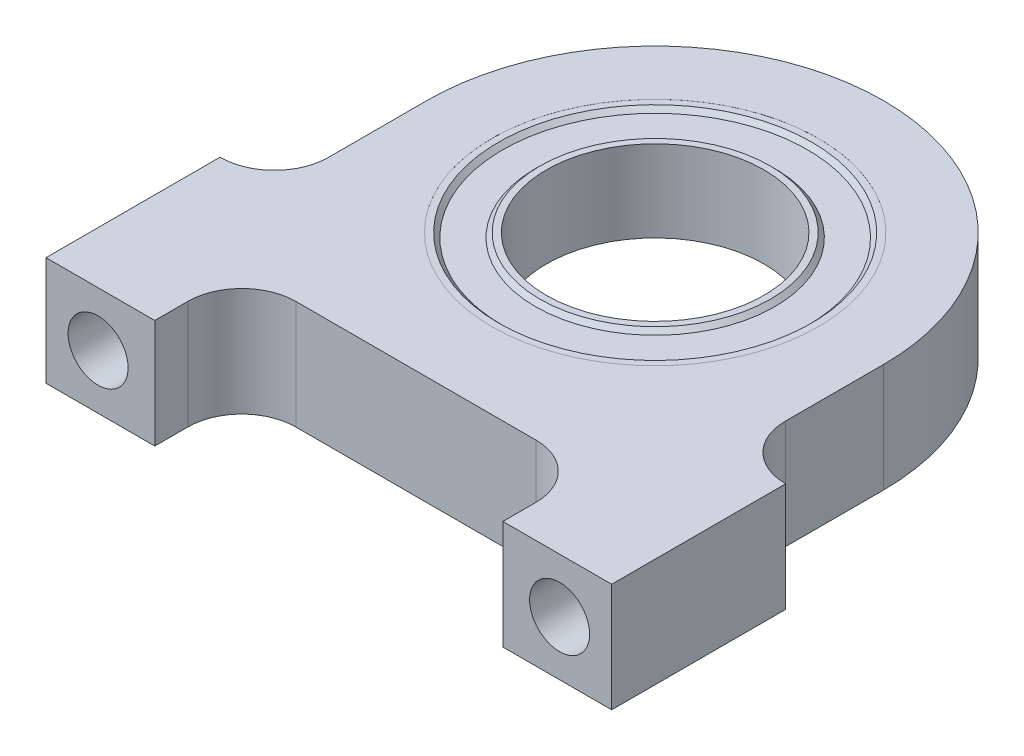
SolidWorks part; units mm, degrees
material "6061 Alloy"
ref_plane "Front Plane" through (0, 0, 0) normal (0, 0, 1) x (1, 0, 0)
ref_plane "Top Plane" through (0, 0, 0) normal (0, 1, 0) x (1, 0, 0)
ref_plane "Right Plane" through (0, 0, 0) normal (1, 0, 0) x (0, 0, -1)
sketch "Sketch1" plane through (0, 0, 0) normal (0, 1, 0) x (1, 0, 0)
  line L0 (0, 13.335) -> (0, -19.05) construction
  line L1 (-13.335, 0) -> (-13.335, -5.7404)
  line L2 (13.335, 0) -> (13.335, -5.7404)
  line L3 (-16.51, -19.05) -> (-10.16, -19.05)
  line L4 (-16.51, -19.05) -> (-16.51, -8.89)
  line L5 (16.51, -19.05) -> (16.51, -8.89)
  line L6 (-16.51, -8.89) -> (-16.4846, -8.89)
  line L7 (16.4846, -8.89) -> (16.51, -8.89)
  line L8 (-10.16, -19.05) -> (-10.16, -17.1196)
  line L9 (-7.0104, -13.97) -> (7.0104, -13.97)
  line L10 (10.16, -17.1196) -> (10.16, -19.05)
  line L11 (10.16, -19.05) -> (16.51, -19.05)
  line L12 (-16.4846, -8.89) -> (16.51, -8.89) construction
  arc A0 (13.335, 0) -> (-13.335, 0) centre (0, 0) ccw
  arc A1 (13.335, -5.7404) -> (16.4846, -8.89) centre (16.4846, -5.7404) ccw
  arc A2 (-13.335, -5.7404) -> (-16.4846, -8.89) centre (-16.4846, -5.7404) cw
  arc A3 (7.0104, -13.97) -> (10.16, -17.1196) centre (7.0104, -17.1196) cw
  arc A4 (-10.16, -17.1196) -> (-7.0104, -13.97) centre (-7.0104, -17.1196) cw
  circle A5 centre (0, 0) radius 8.7312
  point P18 (0, -13.97)
  dimension "D1" = 26.67
  dimension "D6" = 3.1496
  dimension "D9" = 3.1496
  dimension "D10" = 17.4625
  dimension "D2" = 32.385
  dimension "D3" = 33.02
  dimension "D4" = 16.51
  dimension "D5" = 10.16
  dimension "D7" = 5.08
  dimension "D8" = 20.32
extrude "Boss-Extrude1" add sketch "Sketch1" along normal blind 6.35
sketch "Sketch2" plane through (0, 6.35, 0) normal (0, 1, 0) x (1, 0, 0)
  circle A0 centre (0, 0) radius 9.525
  dimension "D1" = 19.05
extrude "Cut-Extrude1" cut sketch "Sketch2" against normal blind 4.7625
ref_plane "Plane1" through (0, 1.5875, 0) normal (0, 1, 0) x (-1, 0, 0)
sketch "Sketch3" plane through (0, 1.5875, 0) normal (0, 1, 0) x (-1, 0, 0)
  circle A0 centre (0, 0) radius 9.525
  circle A1 centre (0, 0) radius 8.89
  dimension "D1" = 0.635
extrude "Boss-Extrude2" add sketch "Sketch3" along normal blind 4.76
chamfer "Chamfer1" distance 0.254 angle 45 1 edges at (0, 6.3475, 8.89)
sketch "Sketch5" plane through (0, 1.5875, 0) normal (0, 1, 0) x (-1, 0, 0)
  circle A0 centre (0, 0) radius 6.35
  circle A1 centre (0, 0) radius 6.985
  dimension "D1" = 12.7
  dimension "D2" = 0.635
extrude "Boss-Extrude3" add sketch "Sketch5" along normal blind 4.76 separate body
chamfer "Chamfer2" distance 0.254 angle 45 2 edges at (0, 6.3475, 6.985) (0, 1.5875, 6.985)
ref_plane "Plane2" through (0, 6.0935, 0) normal (0, 1, 0) x (-1, 0, 0)
sketch "Sketch6" plane through (0, 6.0935, 0) normal (0, 1, 0) x (-1, 0, 0)
  circle A0 centre (0, 0) radius 6.985
  circle A1 centre (0, 0) radius 8.89
extrude "Boss-Extrude4" add sketch "Sketch6" against normal blind 4.252
hole_wizard "#6-32 Tapped Hole1" positions "Sketch9" profile "Sketch8" tap size "#6-32" standard "Ansi Inch"
sketch "Sketch9" plane through (0, 0, 19.05) normal (0, 0, 1) x (1, 0, 0)
  line L0 (-13.4704, 3.175) -> (13.4704, 3.175) construction
  line L1 (13.4704, 3.175) -> (0, 16.6454) construction
  line L2 (0, 16.6454) -> (-13.4704, 3.175) construction
  line L3 (-16.51, 0) -> (-10.16, 0) construction
  point P0 (-13.4704, 3.175)
  point P1 (13.4704, 3.175)
  dimension "D1" = 3.175
  dimension "D2" = 19.05
  dimension "D3" = 19.05
sketch "Sketch8" plane through (-13.4704, 3.175, 19.05) normal (1, 0, 0) x (0, -1, 0)
  line L0 (0, 0) -> (0, 10.2107)
  line L1 (0, 10.2107) -> (1.3525, 9.398)
  line L2 (1.3525, 9.398) -> (1.3525, 7.0104)
  line L3 (1.3525, 7.0104) -> (1.7526, 7.0104)
  line L4 (1.7526, 7.0104) -> (1.7526, 0)
  line L5 (1.7526, 0) -> (0, 0)
  line L10 (0, 10.2107) -> (-1.3526, 9.398) construction
  line L11 (0, -6.35) -> (0, 107.95) construction
  dimension "Tap Drill Dia." = 2.7051
  dimension "Tap Drill Depth" = 9.398
  dimension "Thread Major Dia." = 3.5052
  dimension "Thread Depth" = 7.0104
  dimension "Drill Angle" = 118
